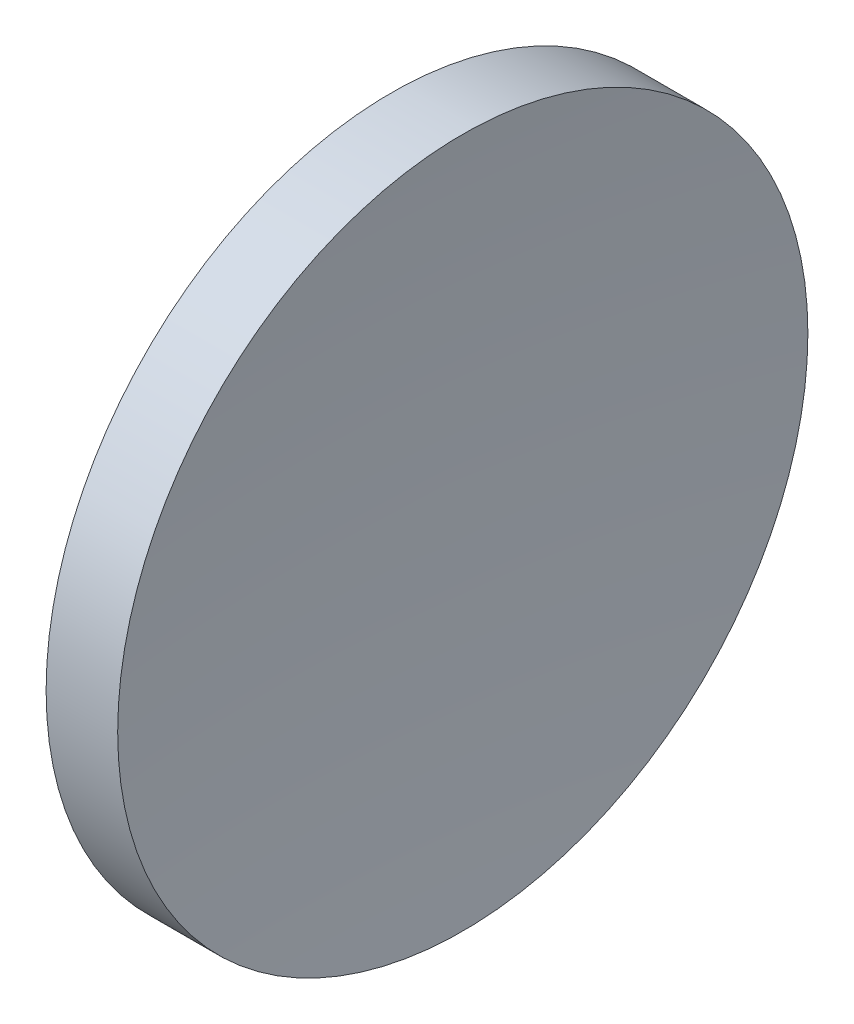
SolidWorks part; units mm, degrees
ref_plane "前视基准面" through (0, 0, 0) normal (0, 0, 1) x (1, 0, 0)
ref_plane "上视基准面" through (0, 0, 0) normal (0, 1, 0) x (1, 0, 0)
ref_plane "右视基准面" through (0, 0, 0) normal (1, 0, 0) x (0, 0, -1)
sketch "草图1" plane through (0, 0, 0) normal (0, 0, 1) x (1, 0, 0)
  line L0 (56.1009, 32.6108) -> (68.2773, 32.6108) construction
  line L1 (57.5323, 32.6108) -> (57.5323, 45.1108)
  line L2 (57.5323, 45.1108) -> (60.1246, 45.1108)
  line L3 (59.5323, 32.6108) -> (57.5323, 32.6108)
  arc A0 (60.1246, 45.1108) -> (59.5323, 32.6108) centre (188.6623, 32.7567) ccw
revolve "旋转1" add sketch "草图1" angle 360 about L0
